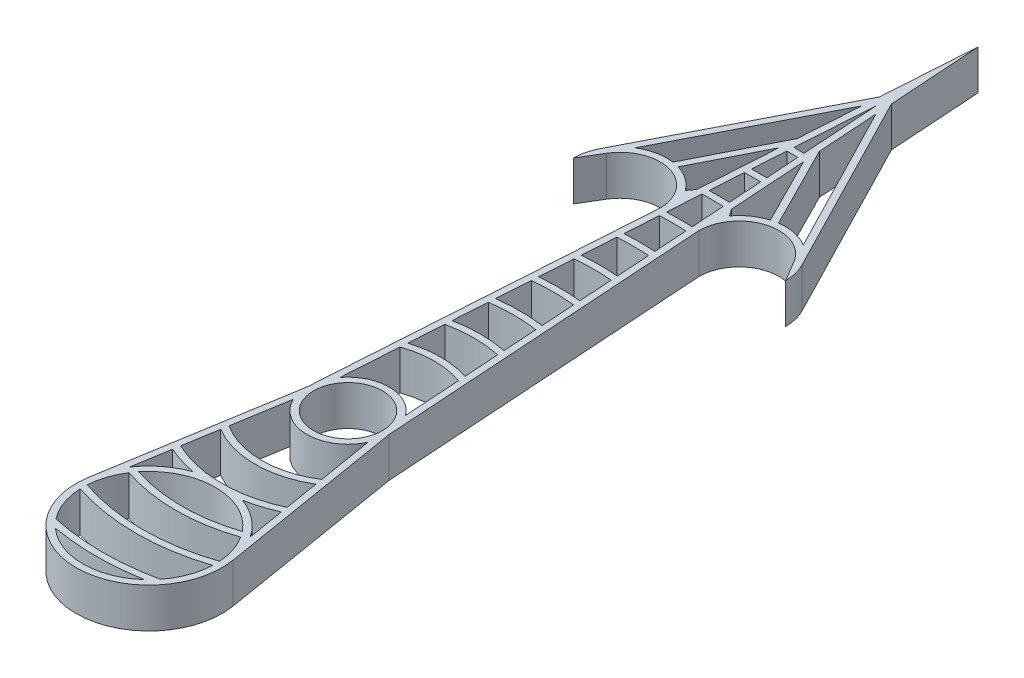
SolidWorks part; units mm, degrees
ref_plane "Front Plane" through (0, 0, 0) normal (0, 0, 1) x (1, 0, 0)
ref_plane "Top Plane" through (0, 0, 0) normal (0, 1, 0) x (1, 0, 0)
ref_plane "Right Plane" through (0, 0, 0) normal (1, 0, 0) x (0, 0, -1)
sketch "Sketch1" plane through (0, 0, 0) normal (0, 1, 0) x (1, 0, 0)
  line L0 (-6.2, 0) -> (0, 95)
  line L1 (0, 95) -> (6.2, 0)
  line L2 (0, 0) -> (0, 95) construction
  line L3 (0, 0) -> (0, -30) construction
  line L4 (-10.8533, -28.2097) -> (-6.2, 0)
  line L5 (6.2, 0) -> (10.8533, -28.2097)
  line L6 (-9.1208, -23.851) -> (-5.6188, -2.6209)
  line L7 (5.6188, -2.6209) -> (9.1208, -23.851)
  line L13 (-4.9546, 3.7272) -> (0, 79.6448)
  line L20 (0, 79.6448) -> (4.9546, 3.7272)
  circle A0 centre (0, 0) radius 5.2
  circle A2 centre (0, -30) radius 10
  arc A3 (9.1208, -23.851) -> (-9.1208, -23.851) centre (0, -30) ccw
  arc A8 (-5.6188, -2.6209) -> (5.6188, -2.6209) centre (0, 0) ccw
  arc A9 (4.9546, 3.7272) -> (-4.9546, 3.7272) centre (0, 0) ccw
  arc A11 (-10.8533, -28.2097) -> (10.8533, -28.2097) centre (0, -30) ccw
  circle A12 centre (0, -30) radius 11 construction
  point P32 (12.432, 3.8008)
  point P33 (0, 0)
  point P34 (18, 0)
  point P35 (0, 0)
  point P36 (13.3883, 4.0932)
  point P39 (0, 0)
  point P40 (23, 0)
  point P42 (0, 0)
  point P43 (19, 0)
  point P45 (28, 0)
  point P46 (0, 0)
  point P47 (24, 0)
  point P48 (0, 0)
  point P49 (33, 0)
  point P50 (0, 0)
  point P52 (0, 0)
  point P53 (38, 0)
  point P54 (0, 0)
  point P56 (0, 0)
  point P57 (43, 0)
  point P58 (0, 0)
  point P59 (39, 0)
  point P60 (0, 0)
  point P61 (48, 0)
  point P62 (0, 0)
  point P63 (44, 0)
  point P64 (0, 0)
  point P65 (53, 0)
  point P66 (0, 0)
  point P67 (49, 0)
  point P68 (0, 0)
  point P69 (58, 0)
  point P70 (0, 0)
  point P71 (54, 0)
  point P72 (0, 0)
  point P73 (63, 0)
  point P74 (0, 0)
  point P75 (59, 0)
  point P76 (64, 0)
  point P84 (10.5194, -26.7839)
  point P116 (34, 0)
  point P130 (29, 0)
  dimension "D1" = 10.4
  dimension "D3" = 6.2
  dimension "D4" = 30
  dimension "D5" = 1
  dimension "D6" = 20
  dimension "D11" = 6.2
  dimension "D2" = 95
  dimension "D7" = 1
  dimension "D8" = 1
  dimension "D10" = 1
  dimension "D9" = 6.2
extrude "Boss-Extrude1" add sketch "Sketch1" along normal blind 6
sketch "Sketch3" plane through (0, 0, 0) normal (0, 1, 0) x (1, 0, 0)
  line L0 (-1.3272, 66.9869) -> (-1.2618, 67.9883)
  line L1 (1.6541, 61.9779) -> (1.7195, 60.9758)
  line L2 (-1.7195, 60.9758) -> (-1.6541, 61.9779)
  line L3 (-10.36, -28.2911) -> (-5.7067, -0.0814)
  line L4 (-5.4536, 3.7597) -> (0, 87.3224)
  line L5 (0, 87.3224) -> (5.4536, 3.7597)
  line L6 (-4.9134, 12.0357) -> (-4.8416, 13.1362)
  line L7 (1.2618, 67.9883) -> (1.3272, 66.9869)
  line L8 (-9.6741, -24.1332) -> (-9.5073, -23.1217)
  line L9 (8.4966, -16.9944) -> (8.6665, -18.0247)
  line L10 (5.7067, -0.0814) -> (10.36, -28.2911)
  line L11 (7.4505, -10.6531) -> (7.6296, -11.7384)
  line L12 (-7.6296, -11.7384) -> (-7.4505, -10.6531)
  line L13 (-8.6665, -18.0247) -> (-8.4966, -16.9944)
  line L14 (9.5073, -23.1217) -> (9.6741, -24.1332)
  line L15 (2.0466, 55.9626) -> (2.1121, 54.9594)
  line L16 (-2.1121, 54.9594) -> (-2.0466, 55.9626)
  line L17 (2.4397, 49.9404) -> (2.5052, 48.9359)
  line L18 (-2.5052, 48.9359) -> (-2.4397, 49.9404)
  line L19 (2.8333, 43.9087) -> (2.899, 42.9022)
  line L20 (-2.899, 42.9022) -> (-2.8333, 43.9087)
  line L21 (3.2279, 37.8627) -> (3.2938, 36.8531)
  line L22 (-3.2938, 36.8531) -> (-3.2279, 37.8627)
  line L23 (3.624, 31.7941) -> (3.6902, 30.7796)
  line L24 (-3.6902, 30.7796) -> (-3.624, 31.7941)
  line L25 (4.0225, 25.6869) -> (4.0893, 24.6633)
  line L26 (4.8416, 13.1362) -> (4.9134, 12.0357)
  line L27 (4.426, 19.5041) -> (4.4941, 18.4608)
  line L28 (-4.0893, 24.6633) -> (-4.0225, 25.6869)
  line L29 (-4.4941, 18.4608) -> (-4.426, 19.5041)
  arc A0 (-7.4505, -10.6531) -> (7.4505, -10.6531) centre (0, 0) ccw
  arc A1 (-7.6296, -11.7384) -> (7.6296, -11.7384) centre (0, 0) ccw
  arc A2 (-8.4966, -16.9944) -> (8.4966, -16.9944) centre (0, 0) ccw
  arc A3 (-8.6665, -18.0247) -> (8.6665, -18.0247) centre (0, 0) ccw
  arc A4 (-9.5073, -23.1217) -> (9.5073, -23.1217) centre (0, 0) ccw
  arc A5 (-9.6741, -24.1332) -> (9.6741, -24.1332) centre (0, 0) ccw
  arc A6 (-10.4975, -30.2292) -> (10.4975, -30.2292) centre (0, 0) ccw
  arc A7 (-10.4679, -29.1792) -> (10.4679, -29.1792) centre (0, 0) ccw
  arc A8 (-7.6151, -37.2292) -> (7.6151, -37.2292) centre (0, 0) ccw
  arc A9 (-8.6313, -35.9792) -> (8.6313, -35.9792) centre (0, 0) ccw
  arc A10 (2.8333, 43.9087) -> (-2.8333, 43.9087) centre (0, 0) ccw
  arc A11 (2.899, 42.9022) -> (-2.899, 42.9022) centre (0, 0) ccw
  arc A12 (2.4397, 49.9404) -> (-2.4397, 49.9404) centre (0, 0) ccw
  arc A13 (2.5052, 48.9359) -> (-2.5052, 48.9359) centre (0, 0) ccw
  arc A14 (2.0466, 55.9626) -> (-2.0466, 55.9626) centre (0, 0) ccw
  arc A15 (2.1121, 54.9594) -> (-2.1121, 54.9594) centre (0, 0) ccw
  arc A16 (1.6541, 61.9779) -> (-1.6541, 61.9779) centre (0, 0) ccw
  arc A17 (1.7195, 60.9758) -> (-1.7195, 60.9758) centre (0, 0) ccw
  arc A18 (1.2618, 67.9883) -> (-1.2618, 67.9883) centre (0, 0) ccw
  arc A19 (1.3272, 66.9869) -> (-1.3272, 66.9869) centre (0, 0) ccw
  arc A20 (4.9134, 12.0357) -> (-4.9134, 12.0357) centre (0, 0) ccw
  circle A21 centre (0, 0) radius 26 construction
  circle A22 centre (0, -30) radius 10.5
  arc A23 (-8.308, -23.5792) -> (-8.9003, -24.4292) centre (0, -30) ccw
  circle A24 centre (0, 0) radius 68 construction
  circle A25 centre (0, 0) radius 67 construction
  circle A26 centre (0, 0) radius 62 construction
  circle A27 centre (0, 0) radius 61 construction
  circle A28 centre (0, 0) radius 56 construction
  circle A29 centre (0, 0) radius 55 construction
  circle A30 centre (0, 0) radius 50 construction
  circle A31 centre (0, 0) radius 49 construction
  circle A32 centre (0, 0) radius 44 construction
  circle A33 centre (0, 0) radius 43 construction
  circle A34 centre (0, 0) radius 38 construction
  circle A35 centre (0, 0) radius 37 construction
  circle A36 centre (0, 0) radius 32 construction
  circle A37 centre (0, 0) radius 31 construction
  circle A38 centre (0, 0) radius 25 construction
  circle A39 centre (0, 0) radius 20 construction
  circle A40 centre (0, 0) radius 19 construction
  circle A41 centre (0, 0) radius 14 construction
  circle A42 centre (0, 0) radius 13 construction
  arc A43 (4.8416, 13.1362) -> (-4.8416, 13.1362) centre (0, 0) ccw
  arc A44 (4.4941, 18.4608) -> (-4.4941, 18.4608) centre (0, 0) ccw
  arc A45 (4.426, 19.5041) -> (-4.426, 19.5041) centre (0, 0) ccw
  arc A46 (4.0893, 24.6633) -> (-4.0893, 24.6633) centre (0, 0) ccw
  arc A47 (4.0225, 25.6869) -> (-4.0225, 25.6869) centre (0, 0) ccw
  arc A48 (3.6902, 30.7796) -> (-3.6902, 30.7796) centre (0, 0) ccw
  arc A49 (3.624, 31.7941) -> (-3.624, 31.7941) centre (0, 0) ccw
  arc A50 (3.2938, 36.8531) -> (-3.2938, 36.8531) centre (0, 0) ccw
  arc A51 (3.2279, 37.8627) -> (-3.2279, 37.8627) centre (0, 0) ccw
  arc A52 (7.6151, -37.2292) -> (8.6313, -35.9792) centre (0, -30) ccw
  arc A53 (10.4975, -30.2292) -> (10.4679, -29.1792) centre (0, -30) ccw
  arc A54 (-8.6313, -35.9792) -> (-7.6151, -37.2292) centre (0, -30) ccw
  arc A55 (-10.4679, -29.1792) -> (-10.4975, -30.2292) centre (0, -30) ccw
  arc A56 (8.9003, -24.4292) -> (8.308, -23.5792) centre (0, -30) ccw
  point P3 (12.432, 3.8008)
  point P8 (13.3883, 4.0932)
  point P10 (19, 0)
  point P12 (20, 0)
  point P14 (25, 0)
  point P16 (31, 0)
  point P18 (26, 0)
  point P20 (37, 0)
  point P22 (32, 0)
  point P24 (43, 0)
  point P26 (38, 0)
  point P28 (49, 0)
  point P30 (44, 0)
  point P32 (55, 0)
  point P34 (50, 0)
  point P36 (61, 0)
  point P38 (56, 0)
  point P40 (67, 0)
  point P42 (62, 0)
  point P43 (68, 0)
  dimension "D2" = 1
  dimension "D3" = 26
  dimension "D1" = 0.5
  dimension "D4" = 6
  dimension "D5" = 6
  dimension "D6" = 6
  dimension "D7" = 6
  dimension "D8" = 6
  dimension "D9" = 6
  dimension "D10" = 6
  dimension "D11" = 6
  dimension "D12" = 6
  dimension "D13" = 0.5
  dimension "D14" = 0.5
  dimension "D15" = 0.5
extrude "Boss-Extrude2" add sketch "Sketch3" along normal blind 6 contours L26 A43 L6 A20 | L27 A45 L29 A44 | L25 A47 L28 A46 | L23 A49 L24 A48 | L21 A51 L22 A50 | A11 L19 A10 L20 | A13 L17 A12 L18 | A15 L15 A14 L16 | A17 L1 A16 L2 | A19 L7 A18 L0 | L12 A1 L11 A0 | L13 A3 L9 A2 | A5 A56 A4 A23 | A7 A55 A6 A53 | A9 A54 A8 A52
sketch "Sketch5" plane through (0, 0, 0) normal (0, 1, 0) x (1, 0, 0)
  line L0 (16, 50) -> (14.1422, 53.1003)
  line L1 (3.3251, 54.1947) -> (2.0456, 55.9787)
  line L2 (0, 95) -> (6.2, 0) construction
  line L3 (1.9224, 57.8663) -> (3.9974, 54.9731)
  line L4 (-1.5445, 55.9787) -> (-1.2176, 60.9878) construction
  line L5 (1.0952, 70.5405) -> (7.962, 56.9592)
  line L6 (0.5011, 79.6448) -> (12.6785, 55.9731)
  line L7 (0.3377, 82.1485) -> (15.2211, 53.2166)
  line L8 (-0.7603, 67.9957) -> (6.4453, 67.9957) construction
  line L9 (0, 79.6448) -> (7.9605, 79.6448) construction
  line L10 (6.9539, 56.7368) -> (1.2613, 67.9957)
  line L13 (1.9368, 50) -> (2.9368, 50)
  line L14 (0, 0) -> (0, 120.5281) construction
  line L16 (-0.4989, 94.9674) -> (5.7011, -0.0326)
  line L17 (-0.4989, 94.9674) -> (5.7011, -0.0326)
  line L21 (-1.5445, 55.9787) -> (9.1115, 55.9787) construction
  arc A0 (15, 50) -> (2.9368, 50) centre (8.9684, 50) ccw
  arc A1 (16, 50) -> (1.9368, 50) centre (8.9684, 50) ccw
  arc A2 (15, 50) -> (2.9368, 50) centre (8.9684, 50) ccw construction
  arc A3 (1.5445, 55.9787) -> (-1.5445, 55.9787) centre (0, 0) ccw construction
  dimension "D1" = 15
  dimension "D3" = 1
  dimension "D4" = 1
  dimension "D5" = 1
  dimension "D7" = 50
  dimension "D2" = 1
  dimension "D6" = 0.5
extrude "Boss-Extrude4" add sketch "Sketch5" along normal blind 6 contours L0 A1 L17 L13 A0 | A1 L5 L17 L10 | A1 L7 L17 L6 | A1 L1 L17
mirror "Mirror1" about plane through (0, 0, 0) normal (1, 0, 0) of "Boss-Extrude4"
